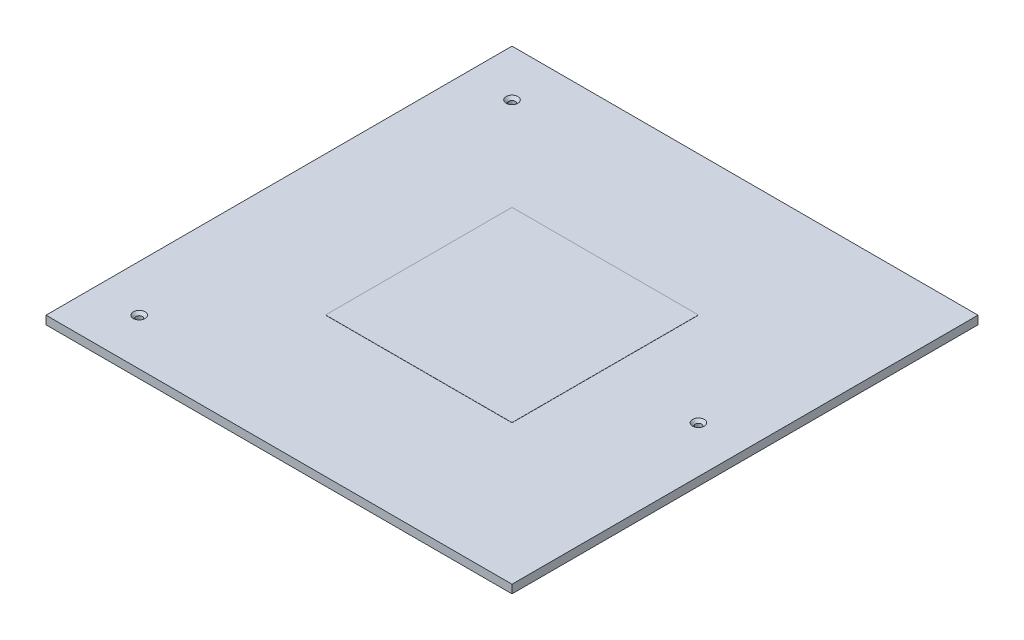
SolidWorks part; units mm, degrees
material "6061 Alloy"
ref_plane "Front Plane" through (0, 0, 0) normal (0, 0, 1) x (1, 0, 0)
ref_plane "Top Plane" through (0, 0, 0) normal (0, 1, 0) x (1, 0, 0)
ref_plane "Right Plane" through (0, 0, 0) normal (1, 0, 0) x (0, 0, -1)
sketch "Sketch1" plane through (0, 0, 0) normal (0, 1, 0) x (1, 0, 0)
  line L0 (0, 0) -> (0, 250)
  line L1 (0, 0) -> (250, 0)
  line L2 (0, 250) -> (250, 250)
  line L3 (250, 0) -> (250, 250)
  dimension "D1" = 250
  dimension "D2" = 250
extrude "Boss-Extrude2" add sketch "Sketch1" along normal blind 4.5
hole_wizard "CSK for M3 Flat Head Machine Screw1" positions "Sketch4" profile "Sketch3" countersink size "M3" standard "ANSI Metric" end condition through all
sketch "Sketch4" plane through (0, 4.5, 0) normal (0, 1, 0) x (1, 0, 0)
  line L0 (0, 0) -> (250, 0) construction
  line L1 (0, 250) -> (0, 0) construction
  line L2 (250, 0) -> (250, 250) construction
  point P0 (25, 25)
  point P2 (25, 225)
  point P4 (225, 125)
  point P11 (250, 125)
  dimension "D1" = 25
  dimension "D2" = 100
  dimension "D3" = 100
  dimension "D4" = 25
  dimension "D5" = 25
sketch "Sketch3" plane through (25, 4.5, -25) normal (1, 0, 0) x (0, 0, 1)
  line L0 (0, 0) -> (0, 4.5)
  line L1 (0, 4.5) -> (1.7, 4.5)
  line L2 (1.7, 4.5) -> (1.7, 1.45)
  line L3 (1.7, 1.45) -> (3.15, 0)
  line L5 (3.15, 0) -> (0, 0)
  line L6 (-1.7, 1.45) -> (-3.15, 0) construction
  line L11 (0, -6.35) -> (0, 107.95) construction
  dimension "Thru Hole Dia." = 3.4
  dimension "Thru Hole Depth" = 4.5
  dimension "Near C'Sink Dia." = 6.3
  dimension "Near C'Sink Angle" = 90
sketch "Sketch5" plane through (0, 4.5, 0) normal (0, 1, 0) x (1, 0, 0)
  line L0 (75, 75) -> (75, 175)
  line L1 (75, 75) -> (175, 75)
  line L2 (75, 175) -> (175, 175)
  line L3 (175, 75) -> (175, 175)
  line L4 (0, 250) -> (0, 0) construction
  line L5 (250, 0) -> (250, 250) construction
  line L6 (250, 250) -> (0, 250) construction
  line L7 (0, 0) -> (250, 0) construction
  point P6 (125, 250)
  dimension "D1" = 75
  dimension "D2" = 75
  dimension "D3" = 75
  dimension "D4" = 75
extrude "Boss-Extrude3" add sketch "Sketch5" along normal blind 0.1
